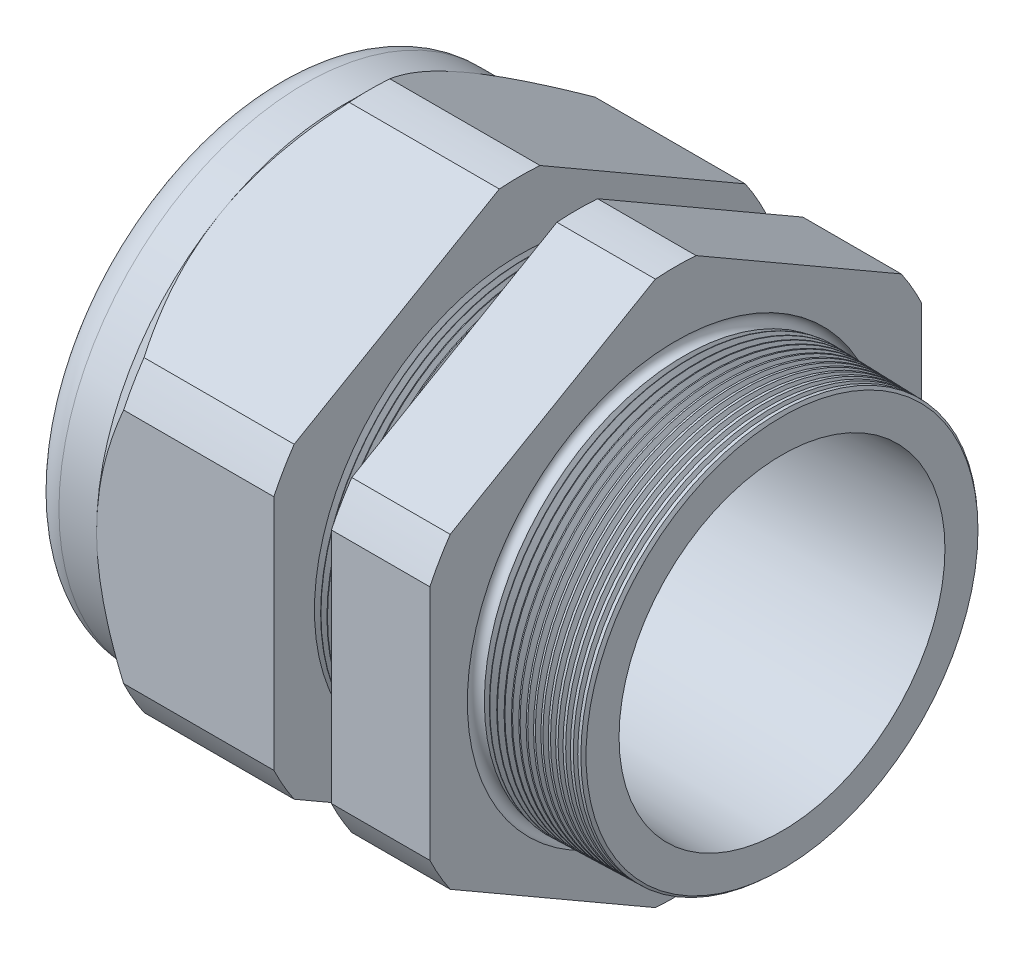
SolidWorks part; units mm, degrees
ref_plane "Front Plane" through (0, 0, 0) normal (0, 0, 1) x (1, 0, 0)
ref_plane "Top Plane" through (0, 0, 0) normal (0, 1, 0) x (1, 0, 0)
ref_plane "Right Plane" through (0, 0, 0) normal (1, 0, 0) x (0, 0, -1)
sketch "Sketch10" plane through (0, 0, 0) normal (0, 0, 1) x (1, 0, 0)
  line L0 (0, 0) -> (-115.3565, 0) construction
  line L1 (-56.896, 19.05) -> (-26.8936, 19.05)
  line L2 (5.08, 19.8637) -> (5.08, 24.1817)
  line L3 (-7.874, 24.521) -> (5.08, 24.1817)
  line L4 (-7.874, 59.944) -> (-7.874, 24.521)
  line L5 (-7.874, 59.944) -> (-19.874, 59.944)
  line L6 (-19.874, 59.944) -> (-19.874, 24.8352)
  line L7 (-26.8936, 25.019) -> (-19.874, 24.8352)
  line L8 (-26.8936, 25.019) -> (-26.8936, 59.944)
  line L9 (-26.8936, 59.944) -> (-48.496, 59.944)
  line L10 (-48.496, 59.944) -> (-48.496, 29.972)
  line L11 (-48.496, 29.972) -> (-56.896, 29.972)
  line L12 (-56.896, 29.972) -> (-56.896, 19.05)
  line L13 (-26.8936, 19.05) -> (5.08, 19.8637)
  dimension "D1" = 61.976
  dimension "D2" = 38.1
  dimension "D3" = 1.5
  dimension "D4" = 4.318
  dimension "A" = 50.038
  dimension "D6" = 59.944
  dimension "D8" = 119.888
  dimension "D9" = 8.4
  dimension "D10" = 21.6024
  dimension "D11" = 12
  dimension "D" = 12.954
revolve "Revolve2" add sketch "Sketch10" angle 360 about L0
sketch "Sketch12" plane through (-48.496, 0, 0) normal (-1, 0, 0) x (0, 0, 1)
  line L1 (-2.481, 33.1763) -> (-27.491, 18.7367)
  line L2 (-29.972, 14.4395) -> (-29.972, -14.4395)
  line L3 (-27.491, -18.7367) -> (-2.481, -33.1763)
  line L4 (2.481, -33.1763) -> (27.491, -18.7367)
  line L5 (29.972, -14.4395) -> (29.972, 14.4395)
  line L6 (27.491, 18.7367) -> (2.481, 33.1763)
  circle A0 centre (0, 0) radius 29.972 construction
  arc A1 (2.481, 33.1763) -> (-2.481, 33.1763) centre (0, 0) ccw
  arc A2 (-27.491, 18.7367) -> (-29.972, 14.4395) centre (0, 0) ccw
  arc A3 (-29.972, -14.4395) -> (-27.491, -18.7367) centre (0, 0) ccw
  arc A4 (-2.481, -33.1763) -> (2.481, -33.1763) centre (0, 0) ccw
  arc A5 (27.491, -18.7367) -> (29.972, -14.4395) centre (0, 0) ccw
  arc A6 (29.972, 14.4395) -> (27.491, 18.7367) centre (0, 0) ccw
  dimension "D2" = 66.5378
  dimension "D1" = 59.944
extrude "Cut-Extrude2" cut sketch "Sketch12" against normal through all flip side to cut
fillet "Fillet4" radius 3.81 1 edges at (-56.896, 0, -29.972)
sketch "Sketch19" plane through (-48.496, 0, 0) normal (-1, 0, 0) x (0, 0, 1)
  line L0 (29.972, 0) -> (29.972, 14.4395) construction
  circle A0 centre (0, 0) radius 29.972
extrude "Cut-Extrude3" cut sketch "Sketch19" against normal blind 3.998 draft 45 flip side to cut
chamfer "Chamfer1" distance 0.254 angle 45 1 edges at (5.08, 0, -24.1817)
sketch "Sketch21" plane through (-56.896, 0, 0) normal (-1, 0, 0) x (0, 0, 1)
  circle A0 centre (0, 0) radius 19.05
  circle A2 centre (0, 0) radius 19.05 construction
extrude "plug" add sketch "Sketch21" against normal blind 11.43 separate body
sketch "Sketch22" plane through (-56.896, 0, 0) normal (-1, 0, 0) x (0, 0, 1)
  circle A0 centre (0, 0) radius 18.796
  circle A1 centre (0, 0) radius 19.05 construction
  dimension "D1" = 0.254
extrude "Cut-Extrude4" cut sketch "Sketch22" against normal blind 0.508
sketch "Sketch27" plane through (-56.388, 0, 0) normal (-1, 0, 0) x (0, 0, 1)
  line L0 (-4.3624, 0) -> (4.3624, 0) construction
  circle A0 centre (-11.7831, 0) radius 6.985
  circle A1 centre (0, 0) radius 18.796 construction
  dimension "D1" = 0.0279
  dimension "holedia" = 13.97
extrude "plugholes" cut sketch "Sketch27" against normal through all
pattern_circular "CirPattern1" count 3 over 360 about axis through (0, 0, 0) along (1, 0, 0) of "plugholes"
sketch "Sketch28" [suppressed] plane through (-29.464, 0, 0) normal (-1, 0, 0) x (0, 0, 1)
  circle A0 centre (0, 0) radius 0.762
  dimension "midholedia" = 13.97
extrude "midhole" [suppressed] cut sketch "Sketch28" against normal through all
sketch "Sketch29" plane through (0, 0, 0) normal (0, 0, 1) x (1, 0, 0)
  line L0 (-26.8936, 25.019) -> (-26.1606, 24.9998)
  line L1 (-19.874, 24.8352) -> (-26.8936, 25.019) construction
  line L2 (-26.1606, 24.9998) -> (-26.5437, 24.3746)
  line L3 (-26.5437, 24.3746) -> (-26.8936, 25.019)
  dimension "D1" = 60
  dimension "D2" = 60
  dimension "D3" = 0.635
revolve "Cut-Revolve1" cut sketch "Sketch29" angle 360 about axis through (0, 0, 0) along (-1, 0, 0)
pattern_linear "LPattern1" count 9 spacing 0.762 along (1, 0, 0) of "Cut-Revolve1"
sketch "Sketch30" plane through (0, 0, 0) normal (0, 0, 1) x (1, 0, 0)
  line L0 (-7.874, 24.521) -> (-6.9944, 24.4979)
  line L1 (-7.874, 33.1763) -> (-7.874, 18.7367) construction
  line L2 (4.8261, 24.1884) -> (-7.874, 24.521) construction
  line L3 (-6.9944, 24.4979) -> (-7.4542, 23.7477)
  line L4 (-7.4542, 23.7477) -> (-7.874, 24.521)
  dimension "D1" = 60
  dimension "D2" = 60
  dimension "D3" = 0.762
revolve "Cut-Revolve2" cut sketch "Sketch30" angle 360 about axis through (0, 0, 0) along (-1, 0, 0)
pattern_linear "LPattern2" count 15 spacing 0.889 along (1, 0, 0) of "Cut-Revolve2"
sketch "Sketch31" [suppressed] plane through (-38.354, 0, 0) normal (-1, 0, 0) x (0, 0, 1)
  line L0 (-1.905, 1.905) -> (1.905, 1.905)
  line L1 (-1.905, -1.905) -> (1.905, -1.905)
  circle A0 centre (0, 0) radius 1.905 construction
  arc A1 (-1.905, 1.905) -> (-1.905, -1.905) centre (-1.905, 0) ccw
  arc A2 (1.905, 1.905) -> (1.905, -1.905) centre (1.905, 0) cw
extrude "Cut-Extrude5" [suppressed] cut sketch "Sketch31" against normal through all
sketch "Sketch32" plane through (0, 0, 0) normal (0, 0, 1) x (1, 0, 0)
  line L0 (-7.874, 33.1763) -> (-7.874, 18.7367) construction
  circle A0 centre (-7.747, 24.521) radius 0.889
  dimension "D2" = 1.778
  dimension "D1" = 0.127
revolve "Cut-Revolve3" cut sketch "Sketch32" angle 360 about axis through (0, 0, 0) along (-1, 0, 0)
